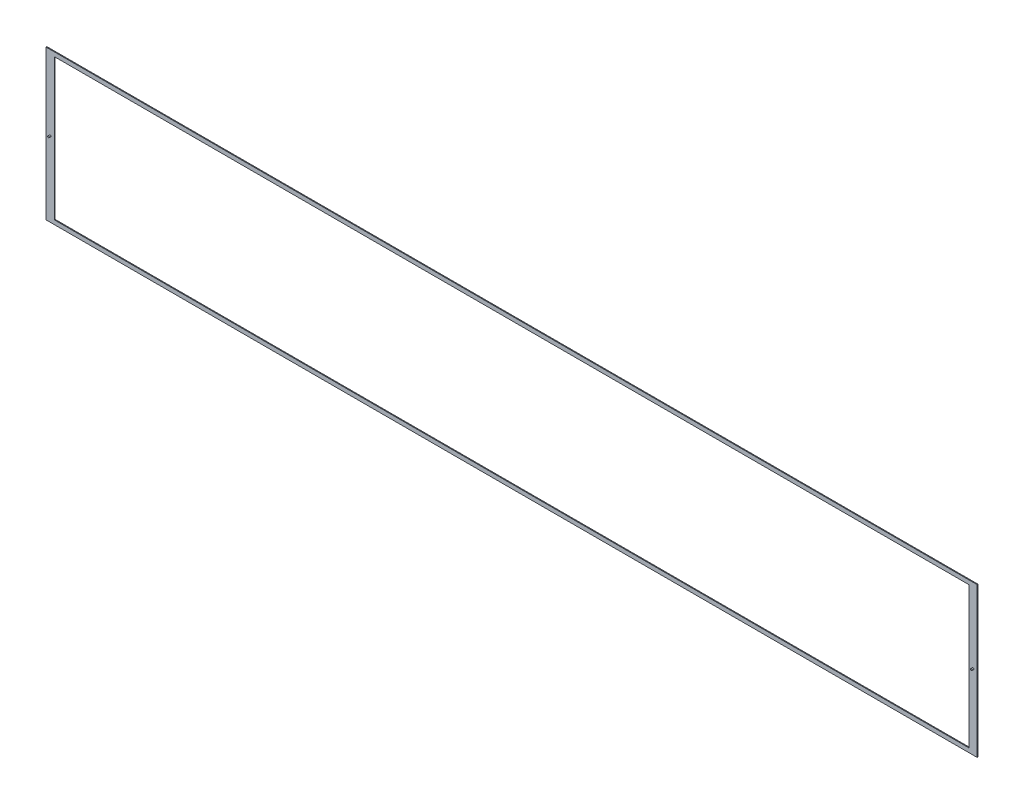
SolidWorks part; units mm, degrees
material "PVC Rigid"
ref_plane "Front Plane" through (0, 0, 0) normal (0, 0, 1) x (1, 0, 0)
ref_plane "Top Plane" through (0, 0, 0) normal (0, 1, 0) x (1, 0, 0)
ref_plane "Right Plane" through (0, 0, 0) normal (1, 0, 0) x (0, 0, -1)
sketch "Sketch1" plane through (0, 0, 0) normal (0, 0, 1) x (1, 0, 0)
  line L1 (-560, -90) -> (560, -90)
  line L2 (-560, -90) -> (-560, 90)
  line L3 (-560, 90) -> (560, 90)
  line L4 (560, -90) -> (560, 90)
  line L5 (-560, -90) -> (560, 90) construction
  line L6 (-560, 90) -> (560, -90) construction
  line L7 (-550, -85) -> (550, -85)
  line L8 (-550, -85) -> (-550, 85)
  line L9 (-550, 85) -> (550, 85)
  line L10 (550, -85) -> (550, 85)
  line L11 (-550, -85) -> (550, 85) construction
  line L12 (-550, 85) -> (550, -85) construction
  point P0 (0, 0)
  point P6 (0, 0)
extrude "Boss-Extrude1" add sketch "Sketch1" along normal blind 1 contours L9 L10 L7 L8 | L3 L4 L1 L2
sketch "Sketch2" plane through (0, 0, 1) normal (0, 0, 1) x (1, 0, 0)
  line L0 (-560, -90) -> (-560, 90) construction
  circle A0 centre (-555, 0) radius 1
  dimension "D1" = 5
extrude "Boss-Extrude2" add sketch "Sketch2" along normal blind 2
mirror "Mirror1" about plane through (0, 0, 0) normal (1, 0, 0) of "Boss-Extrude2"
